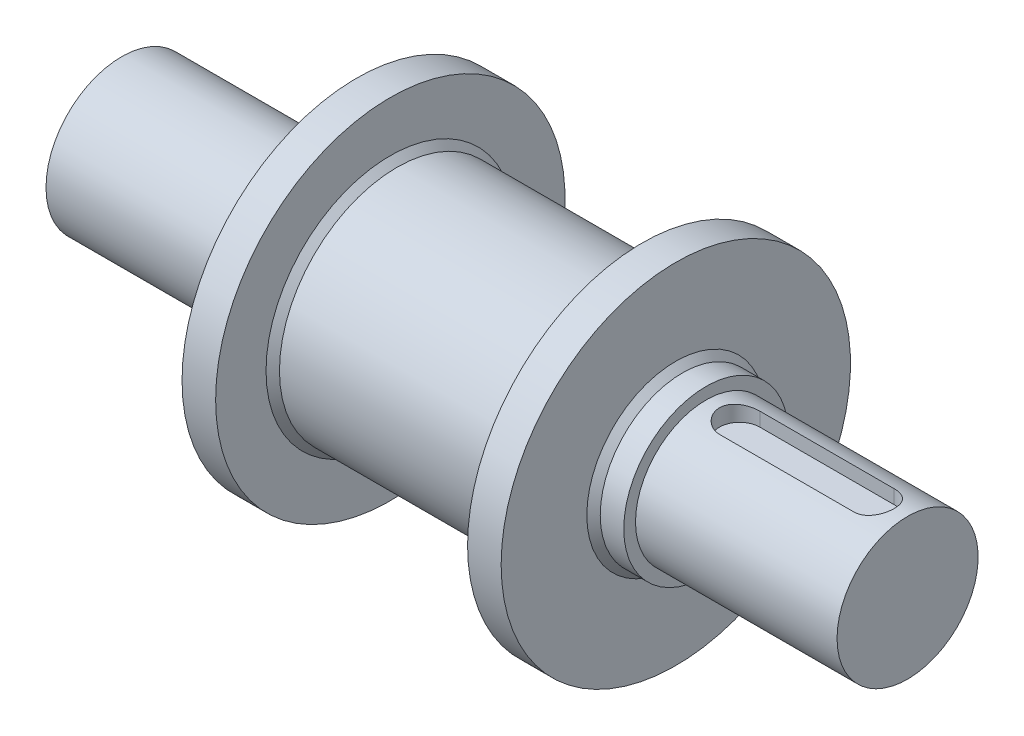
SolidWorks part; units mm, degrees
ref_plane "Front Plane" through (0, 0, 0) normal (0, 0, 1) x (1, 0, 0)
ref_plane "Top Plane" through (0, 0, 0) normal (0, 1, 0) x (1, 0, 0)
ref_plane "Right Plane" through (0, 0, 0) normal (1, 0, 0) x (0, 0, -1)
sketch "Sketch1" plane through (0, 0, 0) normal (0, 0, 1) x (1, 0, 0)
  line L0 (0, 0) -> (0, 22.5)
  line L1 (0, 22.5) -> (65, 22.5)
  line L2 (65, 22.5) -> (65, 27)
  line L3 (65, 27) -> (70, 27)
  line L4 (70, 27) -> (70, 52)
  line L5 (70, 52) -> (80, 52)
  line L6 (80, 52) -> (80, 35)
  line L7 (80, 35) -> (155, 35)
  line L8 (155, 35) -> (155, 52)
  line L9 (155, 52) -> (165, 52)
  line L10 (165, 52) -> (165, 24.5)
  line L11 (165, 24.5) -> (174, 24.5)
  line L14 (174, 24.5) -> (174, 21)
  line L15 (174, 21) -> (234, 21)
  line L16 (234, 21) -> (234, 0)
  line L17 (0, 0) -> (234, 0)
  dimension "D1" = 65
  dimension "D2" = 70
  dimension "D3" = 80
  dimension "D4" = 155
  dimension "D5" = 165
  dimension "D6" = 174
  dimension "D7" = 234
  dimension "D8" = 21
  dimension "D9" = 24.5
  dimension "D10" = 52
  dimension "D11" = 52
  dimension "D12" = 35
  dimension "D13" = 27
  dimension "D14" = 22.5
revolve "Revolve1" add sketch "Sketch1" angle 360 about L17
chamfer "Chamfer1" distance 2 angle 45 3 edges at (165, 0, 24.5) (155, 0, 35) (80, 0, 35)
ref_plane "Plane1" through (0, 21, 0) normal (0, 1, 0) x (1, 0, 0)
sketch "Sketch2" plane through (0, 21, 0) normal (0, 1, 0) x (1, 0, 0)
  line L0 (204, 6) -> (204, -6)
  line L1 (204, -6) -> (184, -6)
  line L2 (204, 6) -> (184, 6)
  line L5 (174, -24.5) -> (174, 24.5) construction
  line L6 (234, 21) -> (174, 21) construction
  arc A0 (184, 6) -> (184, -6) centre (184, 0) ccw
  dimension "D2" = 6
  dimension "D1" = 20
  dimension "D3" = 10
  dimension "D4" = 21
extrude "Cut-Extrude1" cut sketch "Sketch2" against normal blind 5
mirror "Mirror1" about plane through (204, 16, -6) normal (1, 0, 0) of "Cut-Extrude1"
ref_plane "Plane2" through (117.5, 0, 0) normal (1, 0, 0) x (0, 0, -1)
